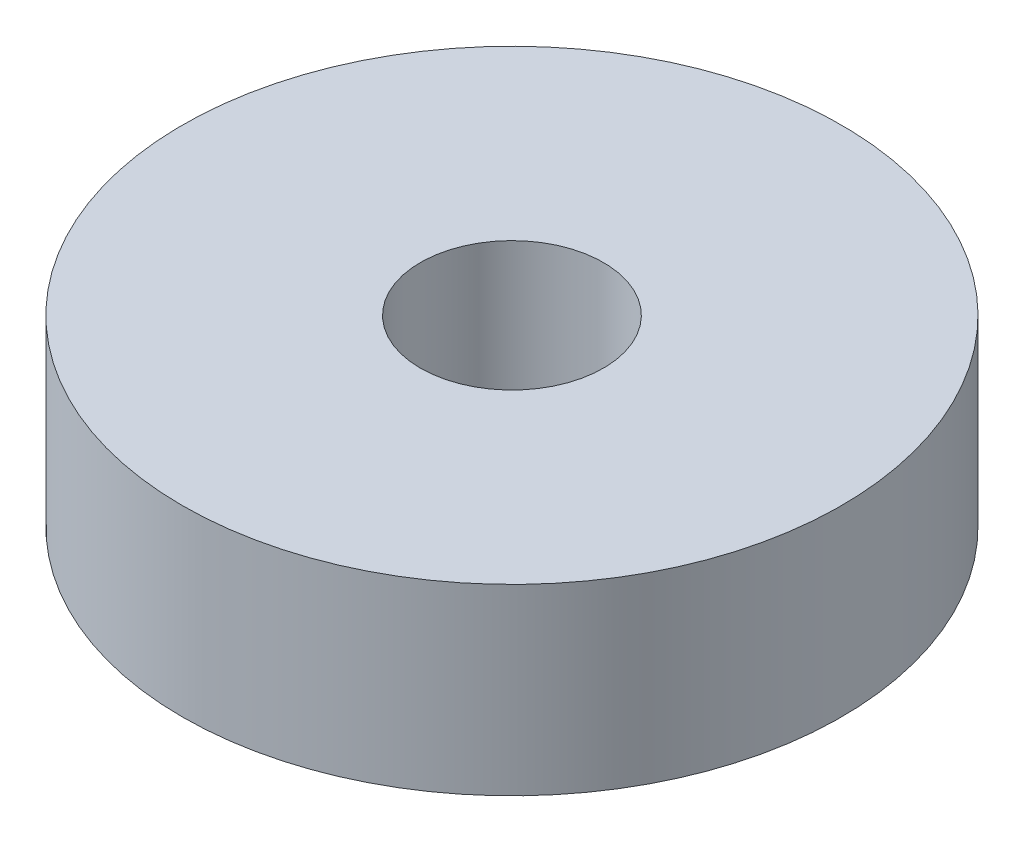
SolidWorks part; units mm, degrees
ref_plane "Front Plane" through (0, 0, 0) normal (0, 0, 1) x (1, 0, 0)
ref_plane "Top Plane" through (0, 0, 0) normal (0, 1, 0) x (1, 0, 0)
ref_plane "Right Plane" through (0, 0, 0) normal (1, 0, 0) x (0, 0, -1)
sketch "Sketch1" plane through (0, 0, 0) normal (0, 1, 0) x (1, 0, 0)
  circle A0 centre (0, 0) radius 2.5
  circle A1 centre (0, 0) radius 9
  dimension "D1" = 5
  dimension "D2" = 18
extrude "Boss-Extrude1" add sketch "Sketch1" along normal blind 5
